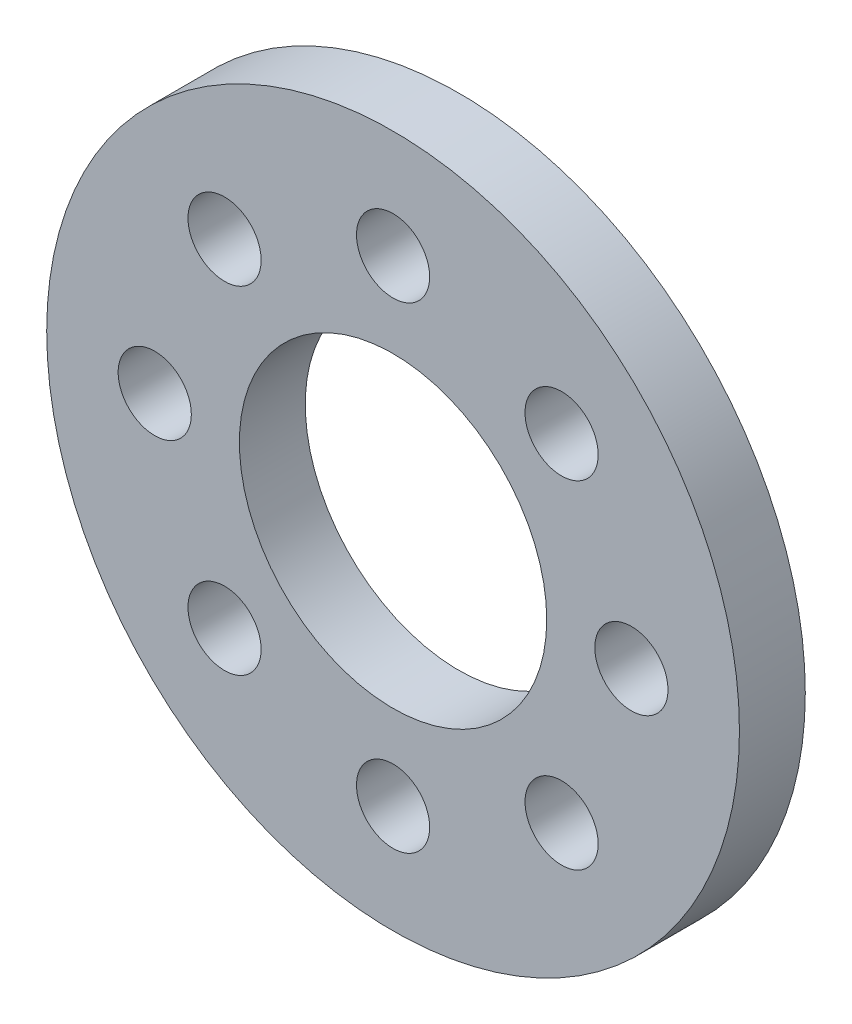
SolidWorks part; units mm, degrees
material "3.0205 (EN-AW 1200)"
ref_plane "Alzado" through (0, 0, 0) normal (0, 0, 1) x (1, 0, 0)
ref_plane "Planta" through (0, 0, 0) normal (0, 1, 0) x (1, 0, 0)
ref_plane "Vista lateral" through (0, 0, 0) normal (1, 0, 0) x (0, 0, -1)
sketch "Croquis1" plane through (0, 0, 0) normal (0, 0, 1) x (1, 0, 0)
  line L0 (0, 14.2) -> (0, -14.2) construction
  circle A0 centre (0, 0) radius 14.2
  circle A1 centre (0, 0) radius 6.3
  circle A2 centre (0, 9.77) radius 1.5
  circle A3 centre (6.9084, 6.9084) radius 1.5
  circle A4 centre (9.77, 0) radius 1.5
  circle A5 centre (6.9084, -6.9084) radius 1.5
  circle A6 centre (0, -9.77) radius 1.5
  circle A7 centre (-6.9084, -6.9084) radius 1.5
  circle A8 centre (-9.77, 0) radius 1.5
  circle A9 centre (-6.9084, 6.9084) radius 1.5
  point P25 (0, 0)
  dimension "D1" = 28.4
  dimension "D2" = 12.6
  dimension "D3" = 3
  dimension "D4" = 9.77
  dimension "D5" = 8
extrude "Saliente-Extruir1" add sketch "Croquis1" along normal blind 2.7
